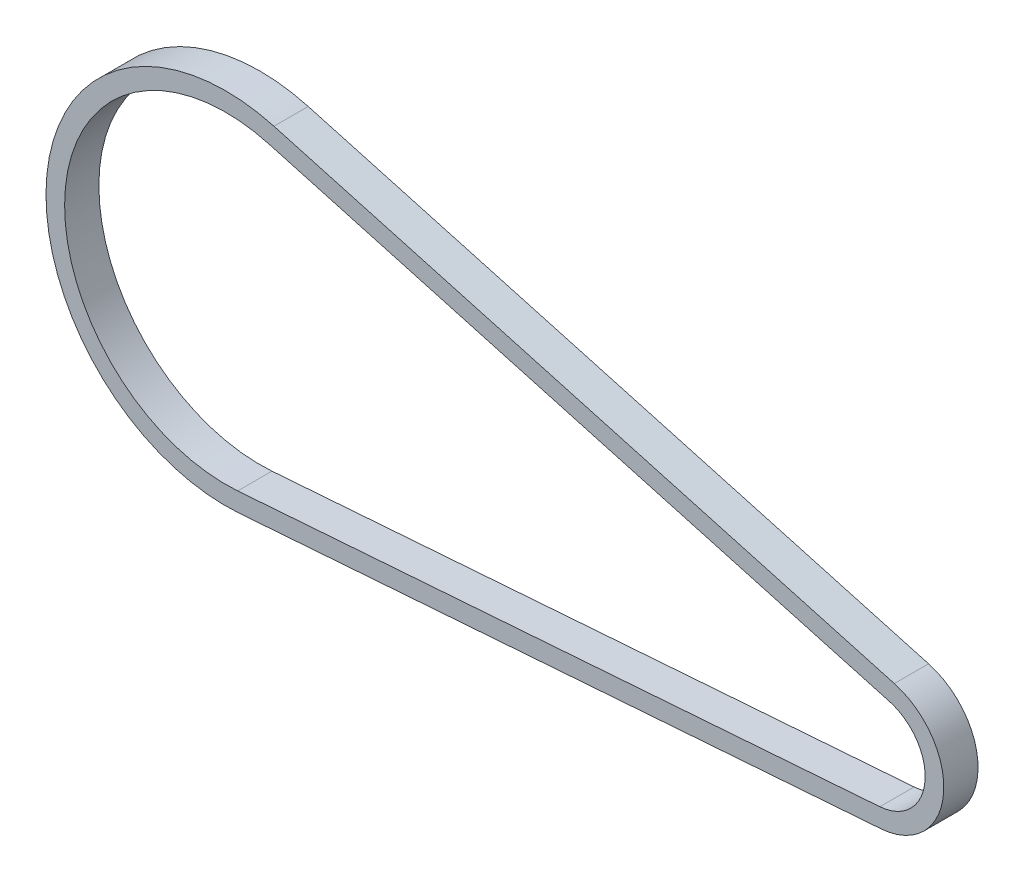
SolidWorks part; units mm, degrees
ref_plane "Front Plane" through (0, 0, 0) normal (0, 0, 1) x (1, 0, 0)
ref_plane "Top Plane" through (0, 0, 0) normal (0, 1, 0) x (1, 0, 0)
ref_plane "Right Plane" through (0, 0, 0) normal (1, 0, 0) x (0, 0, -1)
sketch "Sketch2" plane through (0, 0, 0) normal (0, 0, 1) x (1, 0, 0)
  line L0 (0, 0) -> (1, 0) construction
  line L1 (0, 0) -> (0, 1) construction
  line L2 (33.86, 121.7968) -> (493.8866, -6.0926)
  line L3 (485.5098, -90.7817) -> (9.343, -126.0701)
  arc A0 (9.343, -126.0701) -> (33.86, 121.7968) centre (0, 0) cw
  arc A1 (493.8866, -6.0926) -> (485.5098, -90.7817) centre (482.3175, -47.7071) cw
sketch "Sketch3" plane through (0, 0, 0) normal (1, 0, 0) x (0, 0, -1)
  line L0 (0, 0) -> (0, 126.4158) construction
  line L5 (-12.7, 133.3158) -> (12.7, 133.3158)
  line L6 (-12.7, 133.3158) -> (-12.7, 119.5158)
  line L7 (-12.7, 119.5158) -> (12.7, 119.5158)
  line L8 (12.7, 133.3158) -> (12.7, 119.5158)
  line L9 (-12.7, 133.3158) -> (12.7, 119.5158) construction
  line L10 (-12.7, 119.5158) -> (12.7, 133.3158) construction
  dimension "D1" = 25.4
  dimension "D2" = 13.8
sweep "Sweep1" add profiles "Sketch3" path "Sketch2"
